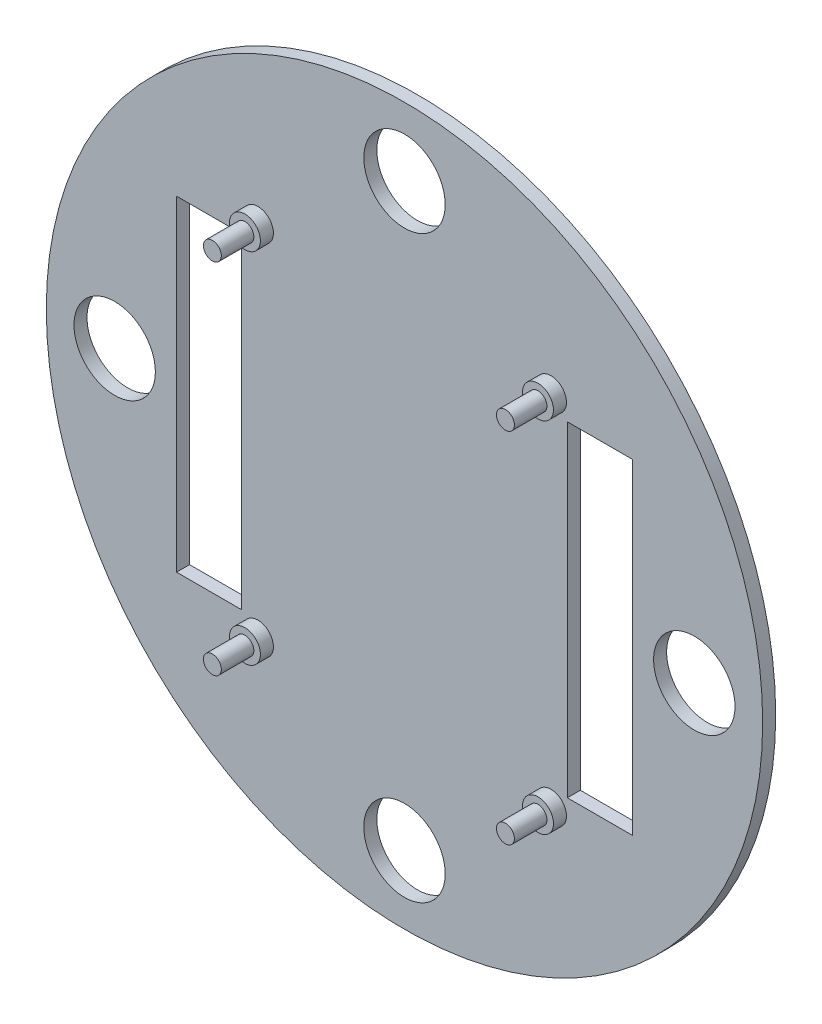
SolidWorks part; units mm, degrees
ref_plane "Front Plane" through (0, 0, 0) normal (0, 0, 1) x (1, 0, 0)
ref_plane "Top Plane" through (0, 0, 0) normal (0, 1, 0) x (1, 0, 0)
ref_plane "Right Plane" through (0, 0, 0) normal (1, 0, 0) x (0, 0, -1)
sketch "Sketch4" plane through (0, 0, 0) normal (0, 0, 1) x (1, 0, 0)
  circle A0 centre (0, 0) radius 59
  dimension "D1" = 118
extrude "Boss-Extrude3" add sketch "Sketch4" along normal blind 2
sketch "Sketch5" plane through (0, 0, 2) normal (0, 0, 1) x (1, 0, 0)
  line L1 (-22.5, 27.5) -> (22.5, 27.5)
  line L2 (-22.5, 27.5) -> (-22.5, -27.5)
  line L3 (-22.5, -27.5) -> (22.5, -27.5)
  line L4 (22.5, 27.5) -> (22.5, -27.5)
  circle A0 centre (0, 0) radius 59 construction
  circle A1 centre (-22.5, 27.5) radius 1.375
  circle A2 centre (22.5, 27.5) radius 1.375
  circle A3 centre (22.5, -27.5) radius 1.375
  circle A4 centre (-22.5, -27.5) radius 1.375
  dimension "D5" = 2.75
  dimension "D6" = 2.75
  dimension "D7" = 2.75
  dimension "D8" = 2.75
  dimension "D1" = 45
  dimension "D2" = 55
  dimension "D3" = 27.5
  dimension "D4" = 22.5
extrude "Boss-Extrude5" add sketch "Sketch5" along normal blind 7 contours A4 | A3 | A2 | A1
sketch "Sketch8" plane through (0, 0, 2) normal (0, 0, 1) x (1, 0, 0)
  circle A4 centre (-22.5, 27.5) radius 2.375
  circle A5 centre (-22.5, 27.5) radius 2.375
  circle A7 centre (22.5, 27.5) radius 2.375
  circle A8 centre (22.5, 27.5) radius 2.375
  circle A10 centre (-22.5, -27.5) radius 2.375
  circle A11 centre (-22.5, -27.5) radius 2.375
  circle A13 centre (22.5, -27.5) radius 2.375
  circle A14 centre (22.5, -27.5) radius 2.375
  dimension "D1" = 1
  dimension "D2" = 1
  dimension "D3" = 1
  dimension "D4" = 1
extrude "Boss-Extrude6" add sketch "Sketch8" along normal blind 2
sketch "Sketch9" plane through (0, 0, 2) normal (0, 0, 1) x (1, 0, 0)
  line L0 (4.7458, 55.7985) -> (5, 58.7878)
  line L1 (55.7985, -4.7458) -> (58.7878, -5)
  line L2 (-4.7458, 55.7985) -> (-5, 58.7878)
  line L3 (55.7985, 4.7458) -> (58.7878, 5)
  line L4 (-4.7458, -55.7985) -> (-5, -58.7878)
  line L5 (4.7458, -55.7985) -> (5, -58.7878)
  line L6 (-55.7985, 4.7458) -> (-58.7878, 5)
  line L7 (-55.7985, -4.7458) -> (-58.7878, -5)
  arc A0 (5, 58.7878) -> (-5, 58.7878) centre (0, 0) ccw
  arc A1 (5, 58.7878) -> (-5, 58.7878) centre (0, 0) ccw
  arc A2 (4.7458, 55.7985) -> (-4.7458, 55.7985) centre (0, 0) ccw
  arc A3 (55.7985, -4.7458) -> (55.7985, 4.7458) centre (0, 0) ccw
  arc A4 (58.7878, -5) -> (58.7878, 5) centre (0, 0) ccw
  arc A5 (-4.7458, -55.7985) -> (4.7458, -55.7985) centre (0, 0) ccw
  arc A6 (-5, -58.7878) -> (5, -58.7878) centre (0, 0) ccw
  arc A7 (-55.7985, 4.7458) -> (-55.7985, -4.7458) centre (0, 0) ccw
  arc A8 (-58.7878, 5) -> (-58.7878, -5) centre (0, 0) ccw
  point P25 (0, 0)
  circle M7 centre (0, 0) radius 59
  dimension "D1" = 118
  dimension "D2" = 3
  dimension "D3" = 4
extrude "Boss-Extrude7" add sketch "Sketch9" along normal blind 18 contours A2 L0 L2 M7 | A7 L6 L7 M7 | A4 L3 A3 L1 | A5 L5 A6 L4
sketch "Sketch10" plane through (0, 0, 2) normal (0, 0, 1) x (1, 0, 0)
  circle A0 centre (-40, 0) radius 7.5
  dimension "D1" = 15
  dimension "D2" = 40
extrude "Cut-Extrude1" cut sketch "Sketch10" against normal blind 18 contours A0
sketch "Sketch12" plane through (0, 0, 20) normal (0, 0, 1) x (1, 0, 0)
  circle A0 centre (0, 0) radius 57.5
  arc A1 (4.7458, 55.7985) -> (-4.7458, 55.7985) centre (0, 0) ccw construction
  dimension "D1" = 1.5
extrude "Cut-Extrude2" cut sketch "Sketch12" against normal blind 5
sketch "Sketch13" plane through (0, 0, 0) normal (0, 0, -1) x (-1, 0, 0)
  line L0 (-58.6183, 6.9928) -> (-53.5993, 6.5659)
  line L1 (-53.5993, -6.5659) -> (-58.6183, -6.9928)
  line L2 (6.9928, 58.6183) -> (6.5659, 53.5993)
  line L3 (-6.5659, 53.5993) -> (-6.9928, 58.6183)
  line L4 (58.6183, -6.9928) -> (53.5993, -6.5659)
  line L5 (53.5993, 6.5659) -> (58.6183, 6.9928)
  line L6 (-6.9928, -58.6183) -> (-6.5659, -53.5993)
  line L7 (6.5659, -53.5993) -> (6.9928, -58.6183)
  line L8 (5, 58.7878) -> (4.7458, 55.7985) construction
  line L9 (-4.7458, 55.7985) -> (-5, 58.7878) construction
  line L10 (55.7985, 4.7458) -> (58.7878, 5) construction
  line L11 (58.7878, -5) -> (55.7985, -4.7458) construction
  line L12 (4.7458, -55.7985) -> (5, -58.7878) construction
  line L13 (-5, -58.7878) -> (-4.7458, -55.7985) construction
  line L14 (-55.7985, -4.7458) -> (-58.7878, -5) construction
  line L15 (-58.7878, 5) -> (-55.7985, 4.7458) construction
  line L16 (4.7458, -55.7985) -> (5, -58.7878)
  line L17 (-5, -58.7878) -> (-4.7458, -55.7985)
  line L18 (-55.7985, -4.7458) -> (-58.7878, -5)
  line L19 (-58.7878, 5) -> (-55.7985, 4.7458)
  line L20 (-4.7458, 55.7985) -> (-5, 58.7878)
  line L21 (5, 58.7878) -> (4.7458, 55.7985)
  line L22 (55.7985, 4.7458) -> (58.7878, 5)
  line L23 (58.7878, -5) -> (55.7985, -4.7458)
  line L24 (4.8686, -57.2433) -> (5, -58.7878)
  line L25 (-5, -58.7878) -> (-4.8686, -57.2433)
  line L26 (-57.2433, -4.8686) -> (-58.7878, -5)
  line L27 (-58.7878, 5) -> (-57.2433, 4.8686)
  line L28 (-4.8686, 57.2433) -> (-5, 58.7878)
  line L29 (5, 58.7878) -> (4.8686, 57.2433)
  line L30 (57.2433, 4.8686) -> (58.7878, 5)
  line L31 (58.7878, -5) -> (57.2433, -4.8686)
  arc A0 (4.8686, 57.2433) -> (-4.8686, 57.2433) centre (0, 0) ccw
  circle A1 centre (0, 0) radius 59
  arc A2 (58.7878, -5) -> (58.7878, 5) centre (0, 0) ccw
  arc A3 (57.2433, -4.8686) -> (57.2433, 4.8686) centre (0, 0) ccw
  arc A4 (-4.8686, -57.2433) -> (4.8686, -57.2433) centre (0, 0) ccw
  arc A5 (-53.5993, 6.5659) -> (-53.5993, -6.5659) centre (0, 0) ccw
  arc A6 (6.5659, 53.5993) -> (-6.5659, 53.5993) centre (0, 0) ccw
  arc A7 (53.5993, -6.5659) -> (53.5993, 6.5659) centre (0, 0) ccw
  arc A8 (-6.5659, -53.5993) -> (6.5659, -53.5993) centre (0, 0) ccw
  circle A9 centre (0, 0) radius 59
  arc A10 (-5, -58.7878) -> (5, -58.7878) centre (0, 0) ccw
  arc A11 (-58.7878, 5) -> (-58.7878, -5) centre (0, 0) ccw
  arc A13 (-57.2433, 4.8686) -> (-57.2433, -4.8686) centre (0, 0) ccw
  arc A18 (5, -58.7878) -> (58.7878, -5) centre (0, 0) ccw
  arc A19 (-4.7458, -55.7985) -> (4.7458, -55.7985) centre (0, 0) ccw
  arc A20 (-58.7878, -5) -> (-5, -58.7878) centre (0, 0) ccw
  arc A21 (-55.7985, 4.7458) -> (-55.7985, -4.7458) centre (0, 0) ccw
  arc A22 (-5, 58.7878) -> (-58.7878, 5) centre (0, 0) ccw
  arc A23 (4.7458, 55.7985) -> (-4.7458, 55.7985) centre (0, 0) ccw
  arc A24 (58.7878, 5) -> (5, 58.7878) centre (0, 0) ccw
  arc A25 (55.7985, -4.7458) -> (55.7985, 4.7458) centre (0, 0) ccw
  arc A34 (4.7458, 55.7985) -> (-4.7458, 55.7985) centre (0, 0) ccw construction
  arc A35 (55.7985, -4.7458) -> (55.7985, 4.7458) centre (0, 0) ccw construction
  arc A36 (-4.7458, -55.7985) -> (4.7458, -55.7985) centre (0, 0) ccw construction
  arc A37 (-55.7985, 4.7458) -> (-55.7985, -4.7458) centre (0, 0) ccw construction
  dimension "D1" = 0
  dimension "D2" = 0
  dimension "D4" = 2
  dimension "D5" = 2
extrude "Cut-Extrude3" cut sketch "Sketch13" against normal blind 5.5
sketch "Sketch15" plane through (0, 0, 0) normal (0, 0, -1) x (-1, 0, 0)
  circle A0 centre (0, 0) radius 57
  circle A1 centre (0, 0) radius 89.714
  dimension "D1" = 114
extrude "Cut-Extrude4" cut sketch "Sketch15" against normal blind 22
sketch "Sketch16" plane through (0, 0, 2) normal (0, 0, 1) x (1, 0, 0)
  line L8 (55.7985, 4.7458) -> (56.7949, 4.8305)
  line L9 (4.8305, 56.7949) -> (4.7458, 55.7985)
  line L10 (-4.7458, 55.7985) -> (-4.8305, 56.7949)
  line L11 (-56.7949, 4.8305) -> (-55.7985, 4.7458)
  line L12 (-55.7985, -4.7458) -> (-56.7949, -4.8305)
  line L13 (-4.8305, -56.7949) -> (-4.7458, -55.7985)
  line L14 (4.7458, -55.7985) -> (4.8305, -56.7949)
  line L15 (56.7949, -4.8305) -> (55.7985, -4.7458)
  line L16 (55.7985, 4.7458) -> (56.7949, 4.8305)
  line L17 (4.8305, 56.7949) -> (4.7458, 55.7985)
  line L18 (-4.7458, 55.7985) -> (-4.8305, 56.7949)
  line L19 (-56.7949, 4.8305) -> (-55.7985, 4.7458)
  line L20 (-55.7985, -4.7458) -> (-56.7949, -4.8305)
  line L21 (-4.8305, -56.7949) -> (-4.7458, -55.7985)
  line L22 (4.7458, -55.7985) -> (4.8305, -56.7949)
  line L23 (56.7949, -4.8305) -> (55.7985, -4.7458)
  circle A0 centre (0, 0) radius 62.462
  arc A8 (56.7949, 4.8305) -> (4.8305, 56.7949) centre (0, 0) ccw
  arc A9 (4.7458, 55.7985) -> (-4.7458, 55.7985) centre (0, 0) ccw
  arc A10 (-4.8305, 56.7949) -> (-56.7949, 4.8305) centre (0, 0) ccw
  arc A11 (-55.7985, 4.7458) -> (-55.7985, -4.7458) centre (0, 0) ccw
  arc A12 (-56.7949, -4.8305) -> (-4.8305, -56.7949) centre (0, 0) ccw
  arc A13 (-4.7458, -55.7985) -> (4.7458, -55.7985) centre (0, 0) ccw
  arc A14 (4.8305, -56.7949) -> (56.7949, -4.8305) centre (0, 0) ccw
  arc A15 (55.7985, -4.7458) -> (55.7985, 4.7458) centre (0, 0) ccw
  arc A16 (56.7949, 4.8305) -> (4.8305, 56.7949) centre (0, 0) ccw
  arc A17 (4.7458, 55.7985) -> (-4.7458, 55.7985) centre (0, 0) ccw
  arc A18 (-4.8305, 56.7949) -> (-56.7949, 4.8305) centre (0, 0) ccw
  arc A19 (-55.7985, 4.7458) -> (-55.7985, -4.7458) centre (0, 0) ccw
  arc A20 (-56.7949, -4.8305) -> (-4.8305, -56.7949) centre (0, 0) ccw
  arc A21 (-4.7458, -55.7985) -> (4.7458, -55.7985) centre (0, 0) ccw
  arc A22 (4.8305, -56.7949) -> (56.7949, -4.8305) centre (0, 0) ccw
  arc A23 (55.7985, -4.7458) -> (55.7985, 4.7458) centre (0, 0) ccw
  dimension "D1" = 0
extrude "Cut-Extrude8" cut sketch "Sketch16" along normal blind 52 contours A0 | L16 A16 L17 A17 L18 A18 L19 A19 L20 A20 L21 A21 L22 A22 L23 A23
sketch "Sketch17" plane through (0, 0, 2) normal (0, 0, 1) x (1, 0, 0)
  line L0 (-5, 57) -> (5, 57)
  line L1 (5, 57) -> (4.8061, 54.7896)
  line L2 (-4.8061, 54.7896) -> (-5, 57)
  line L3 (54.7896, 4.8061) -> (57, 5)
  line L4 (57, 5) -> (57, -5)
  line L5 (57, -5) -> (54.7896, -4.8061)
  line L6 (4.8061, -54.7896) -> (5, -57)
  line L7 (5, -57) -> (-5, -57)
  line L8 (-5, -57) -> (-4.8061, -54.7896)
  line L9 (-54.7896, -4.8061) -> (-57, -5)
  line L10 (-57, -5) -> (-57, 5)
  line L11 (-57, 5) -> (-54.7896, 4.8061)
  arc A0 (4.8061, 54.7896) -> (-4.8061, 54.7896) centre (0, 0) ccw
  circle A1 centre (0, 0) radius 57 construction
  arc A2 (54.7896, -4.8061) -> (54.7896, 4.8061) centre (0, 0) ccw
  arc A3 (-4.8061, -54.7896) -> (4.8061, -54.7896) centre (0, 0) ccw
  arc A4 (-54.7896, 4.8061) -> (-54.7896, -4.8061) centre (0, 0) ccw
  point P8 (0, 57)
  point P24 (0, 0)
  dimension "D1" = 2
  dimension "D2" = 10
  dimension "D3" = 0
  dimension "D4" = 4
extrude "Cut-Extrude9" cut sketch "Sketch17" against normal blind 52
sketch "Sketch18" plane through (0, 0, 2) normal (0, 0, 1) x (1, 0, 0)
  circle A0 centre (0, 0) radius 55
  circle A1 centre (0, 0) radius 80.6225
  dimension "D1" = 110
extrude "Cut-Extrude10" cut sketch "Sketch18" against normal blind 10
sketch "Sketch19" plane through (0, 0, 2) normal (0, 0, 1) x (1, 0, 0)
  circle A0 centre (0, 0) radius 55
extrude "Boss-Extrude8" add sketch "Sketch19" against normal blind 2
sketch "Sketch20" plane through (0, 0, 2) normal (0, 0, 1) x (1, 0, 0)
  line L0 (0, 55) -> (0, -55) construction
  line L1 (-55, 0) -> (55, 0) construction
  circle A0 centre (0, 0) radius 55 construction
  circle A1 centre (0, 0) radius 44.5
  circle A2 centre (0, 44.5) radius 6.25
  circle A3 centre (44.5, 0) radius 6.25
  circle A4 centre (0, -44.5) radius 6.25
  circle A5 centre (-44.5, 0) radius 6.25
  dimension "D1" = 10.5
  dimension "D2" = 12.5
  dimension "D3" = 12.5
  dimension "D4" = 12.5
  dimension "D5" = 12.5
extrude "Cut-Extrude11" cut sketch "Sketch20" against normal blind 2 contours A3 | A2 | A5 | A4
sketch "Sketch21" plane through (0, 0, 2) normal (0, 0, 1) x (1, 0, 0)
  line L1 (25, 25) -> (35, 25)
  line L2 (25, 25) -> (25, -25)
  line L3 (25, -25) -> (35, -25)
  line L4 (35, 25) -> (35, -25)
  line L5 (-35, 25) -> (-25, 25)
  line L6 (-35, 25) -> (-35, -25)
  line L7 (-35, -25) -> (-25, -25)
  line L8 (-25, 25) -> (-25, -25)
  circle A0 centre (0, 0) radius 55 construction
  dimension "D5" = 25
  dimension "D1" = 10
  dimension "D2" = 10
  dimension "D3" = 50
  dimension "D4" = 50
  dimension "D6" = 25
  dimension "D7" = 25
  dimension "D8" = 25
extrude "Cut-Extrude12" cut sketch "Sketch21" against normal blind 3
